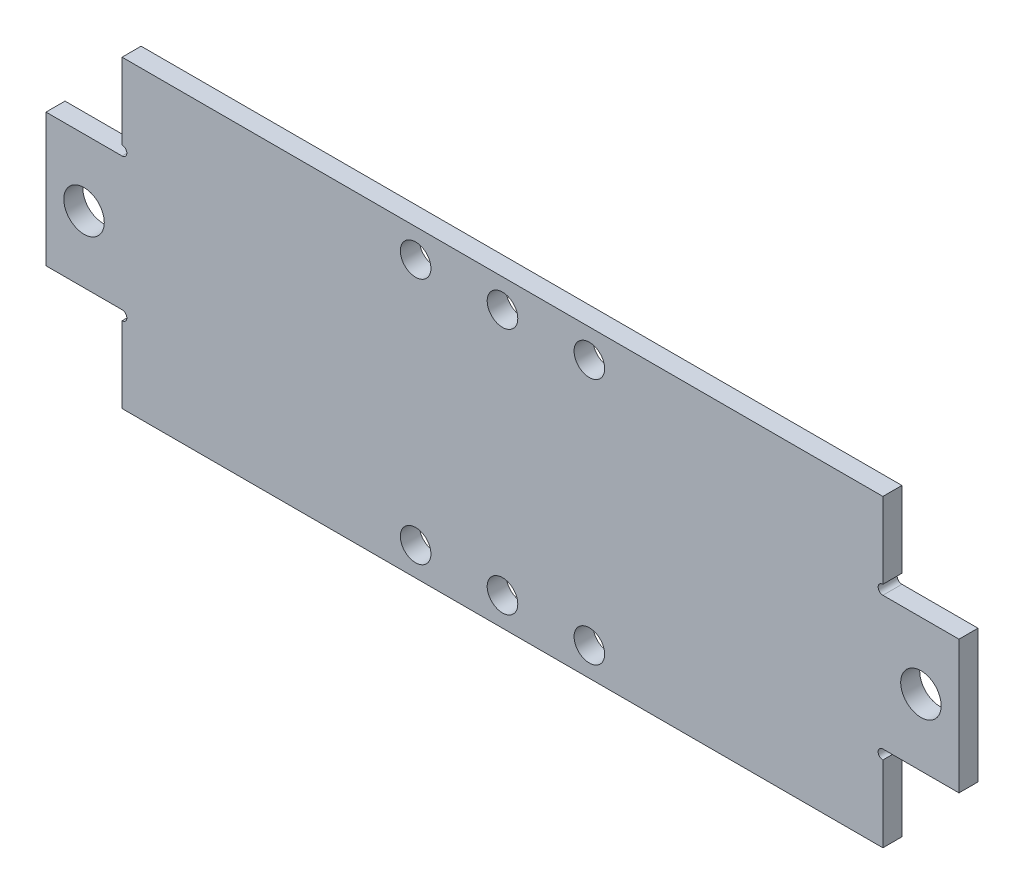
SolidWorks part; units mm, degrees
material "6061-T6 (SS)"
ref_plane "Front Plane" through (0, 0, 0) normal (0, 0, 1) x (1, 0, 0)
ref_plane "Top Plane" through (0, 0, 0) normal (0, 1, 0) x (1, 0, 0)
ref_plane "Right Plane" through (0, 0, 0) normal (1, 0, 0) x (0, 0, -1)
sketch "Sketch1" plane through (0, 0, 0) normal (0, 0, 1) x (1, 0, 0)
  line L1 (0, 0) -> (127, 0)
  line L2 (0, 0) -> (0, 50.8)
  line L3 (0, 50.8) -> (127, 50.8)
  line L4 (127, 0) -> (127, 50.8)
extrude "Boss-Extrude1" add sketch "Sketch1" along normal blind 3.175
sketch "Sketch2" plane through (0, 0, 3.175) normal (0, 0, 1) x (1, 0, 0)
  line L0 (0, 50.8) -> (0, 0) construction
  line L1 (0, 36.5125) -> (-12.7, 36.5125)
  line L2 (0, 36.5125) -> (0, 14.2875)
  line L3 (0, 14.2875) -> (-12.7, 14.2875)
  line L4 (-12.7, 36.5125) -> (-12.7, 14.2875)
  line L5 (127, 0) -> (127, 50.8) construction
  line L6 (127, 36.5125) -> (139.7, 36.5125)
  line L7 (127, 36.5125) -> (127, 14.2875)
  line L8 (127, 14.2875) -> (139.7, 14.2875)
  line L9 (139.7, 36.5125) -> (139.7, 14.2875)
  point P12 (0, 25.4)
  dimension "D1" = 22.225
  dimension "D2" = 12.7
extrude "Boss-Extrude2" add sketch "Sketch2" against normal up to surface (3.175 mm away) up to face at (63.5, 25.4, 0)
sketch "Sketch3" plane through (0, 0, 3.175) normal (0, 0, 1) x (1, 0, 0)
  line L0 (0, 50.8) -> (0, 36.5125) construction
  line L1 (0, 14.2875) -> (0, 0) construction
  line L2 (127, 0) -> (127, 14.2875) construction
  line L3 (127, 36.5125) -> (127, 50.8) construction
  circle A0 centre (0, 37.3062) radius 0.7937
  circle A1 centre (0, 13.4938) radius 0.7937
  circle A2 centre (127, 13.4938) radius 0.7938
  circle A3 centre (127, 37.3063) radius 0.7938
  dimension "D1" = 1.5875
extrude "Cut-Extrude1" cut sketch "Sketch3" against normal through all
hole_wizard "1/4 Clearance Hole1" positions "Sketch5" profile "Sketch4" hole size "1/4" standard "ANSI Inch" end condition through all
sketch "Sketch5" plane through (0, 0, 3.175) normal (0, 0, 1) x (1, 0, 0)
  line L0 (-12.7, 25.4) -> (-6.35, 25.4) construction
  line L1 (-12.7, 36.5125) -> (-12.7, 14.2875) construction
  line L2 (-6.35, 25.4) -> (133.35, 25.4) construction
  line L3 (133.35, 25.4) -> (139.7, 25.4) construction
  line L4 (139.7, 14.2875) -> (139.7, 36.5125) construction
  point P0 (-6.35, 25.4)
  point P2 (133.35, 25.4)
  dimension "D1" = 6.35
sketch "Sketch4" plane through (-6.35, 25.4, 3.175) normal (1, 0, 0) x (0, -1, 0)
  line L0 (0, 0) -> (0, 3.1751)
  line L1 (0, 3.1751) -> (3.3782, 3.1751)
  line L2 (3.3782, 3.1751) -> (3.3782, 0)
  line L5 (3.3782, 0) -> (0, 0)
  line L11 (0, -6.35) -> (0, 107.95) construction
  dimension "Thru Hole Dia." = 6.7564
  dimension "Thru Hole Depth" = 3.1751
hole_wizard "#10 Clearance Hole1" positions "Sketch7" profile "Sketch6" hole size "#10" standard "ANSI Inch"
sketch "Sketch7" plane through (0, 0, 3.175) normal (0, 0, 1) x (1, 0, 0)
  line L0 (49, 4.7625) -> (63.5, 4.7625) construction
  line L1 (63.5, 4.7625) -> (78, 4.7625) construction
  line L3 (63.5, 4.7625) -> (63.5, 0) construction
  line L4 (0, 0) -> (127, 0) construction
  point P0 (63.5, 4.7625)
  point P2 (78, 4.7625)
  point P4 (49, 4.7625)
  dimension "D1" = 4.7625
  dimension "D2" = 14.5
sketch "Sketch6" plane through (63.5, 4.7625, 3.175) normal (1, 0, 0) x (0, -1, 0)
  line L0 (0, 0) -> (0, 14.2338)
  line L1 (0, 14.2338) -> (2.5527, 12.7)
  line L2 (2.5527, 12.7) -> (2.5527, 0)
  line L5 (2.5527, 0) -> (0, 0)
  line L10 (0, 14.2338) -> (-2.5527, 12.7) construction
  line L11 (0, -6.35) -> (0, 107.95) construction
  dimension "Hole Dia." = 5.1054
  dimension "Hole Depth" = 12.7
  dimension "Drill Angle" = 118
ref_plane "Plane1" through (0, 25.4, 0) normal (0, -1, 0) x (-1, 0, 0)
mirror "Mirror1" about plane through (0, 25.4, 0) normal (0, -1, 0) of "#10 Clearance Hole1"
